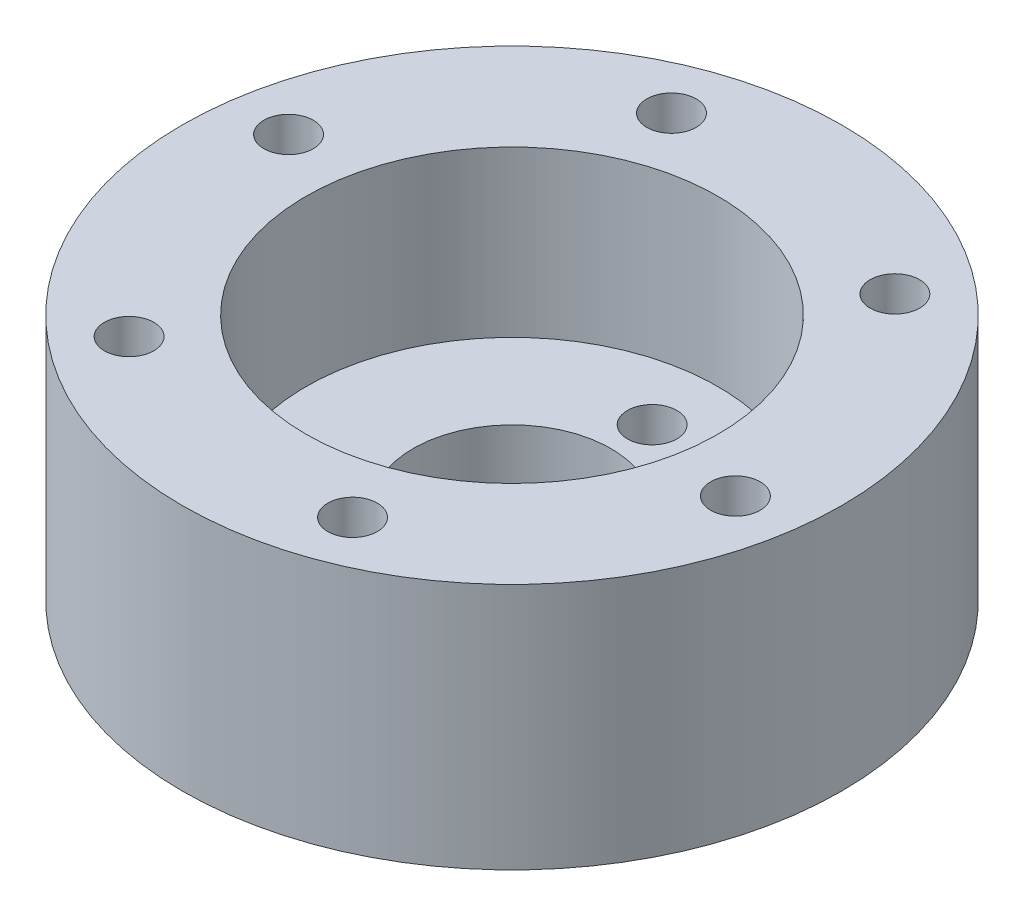
SolidWorks part; units mm, degrees
ref_plane "Front Plane" through (0, 0, 0) normal (0, 0, 1) x (1, 0, 0)
ref_plane "Top Plane" through (0, 0, 0) normal (0, 1, 0) x (1, 0, 0)
ref_plane "Right Plane" through (0, 0, 0) normal (1, 0, 0) x (0, 0, -1)
sketch "Sketch1" plane through (0, 0, 0) normal (0, 1, 0) x (1, 0, 0)
  circle A0 centre (0, 0) radius 20
  dimension "D1" = 40
extrude "Boss-Extrude1" add sketch "Sketch1" along normal blind 15
sketch "Sketch2" plane through (0, 15, 0) normal (0, 1, 0) x (1, 0, 0)
  circle A0 centre (0, 0) radius 12.5
  dimension "D1" = 25
extrude "Cut-Extrude1" cut sketch "Sketch2" against normal blind 10
sketch "Sketch3" plane through (0, 5, 0) normal (0, 1, 0) x (1, 0, 0)
  circle A0 centre (0, 0) radius 6
  dimension "D1" = 12
extrude "Cut-Extrude2" cut sketch "Sketch3" against normal blind 5
sketch "Sketch4" plane through (0, 15, 0) normal (0, 1, 0) x (1, 0, 0)
  circle A0 centre (-10.4931, -12.7336) radius 1.5
  circle A2 centre (-16.2742, 2.7205) radius 1.5
  circle A3 centre (-5.781, 15.4541) radius 1.5
  circle A4 centre (10.4931, 12.7336) radius 1.5
  circle A5 centre (16.2742, -2.7205) radius 1.5
  circle A6 centre (5.781, -15.4541) radius 1.5
  point P16 (0, 0)
  dimension "D2" = 3
  dimension "D3" = 6
  dimension "D1" = 16.5
extrude "Cut-Extrude3" cut sketch "Sketch4" against normal blind 15
sketch "Sketch5" plane through (0, 0, 0) normal (0, -1, 0) x (1, 0, 0)
  circle A0 centre (0, 8.5) radius 1.5
  circle A1 centre (0, -8.5) radius 1.5
  point P7 (0, 0)
  dimension "D1" = 3
  dimension "D2" = 8.5
  dimension "D3" = 2
extrude "Cut-Extrude4" cut sketch "Sketch5" against normal blind 5
